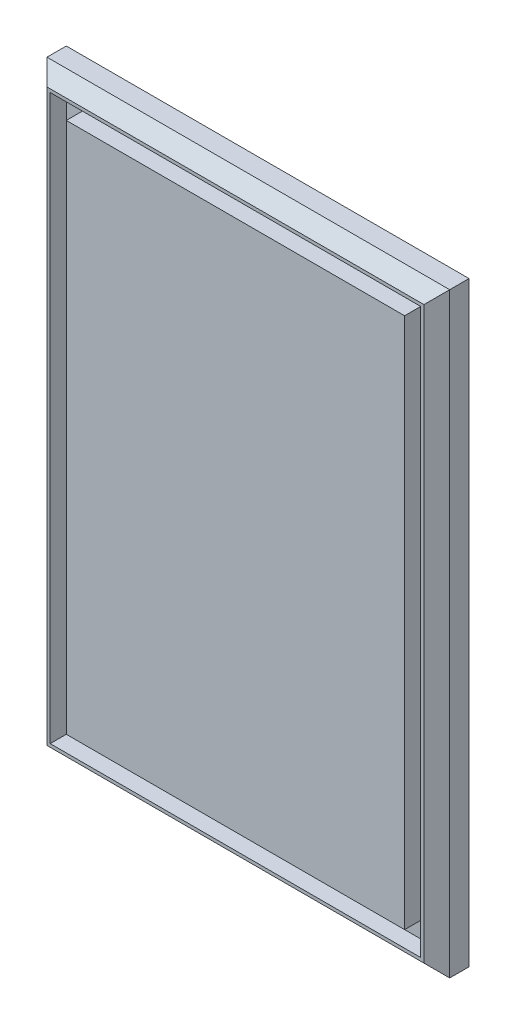
SolidWorks part; units mm, degrees
ref_plane "Спереди" through (0, 0, 0) normal (0, 0, 1) x (1, 0, 0)
ref_plane "Сверху" through (0, 0, 0) normal (0, 1, 0) x (1, 0, 0)
ref_plane "Справа" through (0, 0, 0) normal (1, 0, 0) x (0, 0, -1)
sketch "Эскиз1" plane through (0, 0, 0) normal (0, 0, 1) x (1, 0, 0)
  line L1 (-125, 185) -> (125, 185)
  line L2 (-125, 185) -> (-125, -185)
  line L3 (-125, -185) -> (125, -185)
  line L4 (125, 185) -> (125, -185)
  line L5 (-125, 185) -> (125, -185) construction
  line L6 (-125, -185) -> (125, 185) construction
  point P0 (0, 0)
  dimension "D1" = 250
  dimension "D2" = 370
extrude "Бобышка-Вытянуть1" add sketch "Эскиз1" along normal blind 20 contours L2 L3 L4 L1
chamfer "Фаска1" distance 8 angle 45 4 edges at (125, 0, 20) (0, -185, 20) (-125, 0, 20) (0, 185, 20)
sketch "Эскиз2" plane through (0, 0, 20) normal (0, 0, 1) x (1, 0, 0)
  line L0 (125, 185) -> (125, -185) construction
  line L1 (115, -175) -> (-115, -175)
  line L2 (115, -175) -> (115, 175)
  line L3 (115, 175) -> (-115, 175)
  line L4 (-115, -175) -> (-115, 175)
  line L5 (115, -175) -> (-115, 175) construction
  line L6 (115, 175) -> (-115, -175) construction
  line L7 (-125, 185) -> (125, 185) construction
  line L8 (105, -165) -> (-105, -165)
  line L9 (105, -165) -> (105, 165)
  line L10 (105, 165) -> (-105, 165)
  line L11 (-105, -165) -> (-105, 165)
  line L12 (105, -165) -> (-105, 165) construction
  line L13 (105, 165) -> (-105, -165) construction
  point P0 (0, 0)
  point P8 (0, 0)
  dimension "D1" = 10
  dimension "D2" = 10
  dimension "D3" = 10
  dimension "D4" = 10
extrude "Вырез-Вытянуть1" cut sketch "Эскиз2" against normal blind 10
